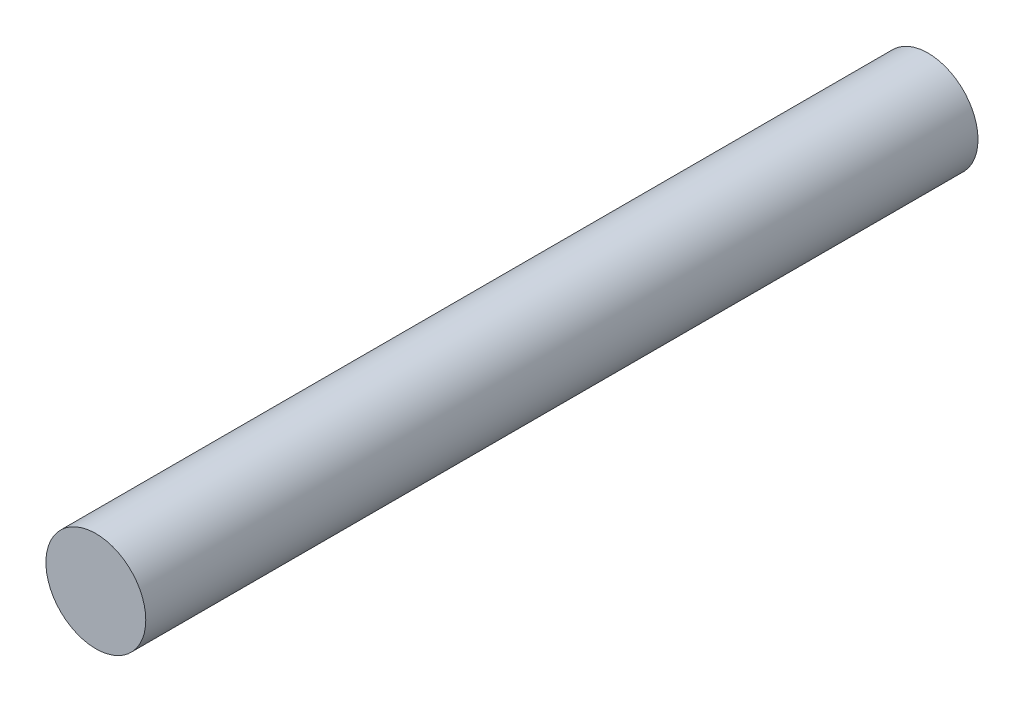
SolidWorks part; units mm, degrees
ref_plane "Plano frontal" through (0, 0, 0) normal (0, 0, 1) x (1, 0, 0)
ref_plane "Plano superior" through (0, 0, 0) normal (0, 1, 0) x (1, 0, 0)
ref_plane "Plano direito" through (0, 0, 0) normal (1, 0, 0) x (0, 0, -1)
sketch "Esboço1" plane through (0, 0, 0) normal (0, 0, 1) x (1, 0, 0)
  circle A0 centre (0, 0) radius 1.5
  dimension "D1" = 3
extrude "Ressalto-extrusão1" add sketch "Esboço1" along normal blind 25
